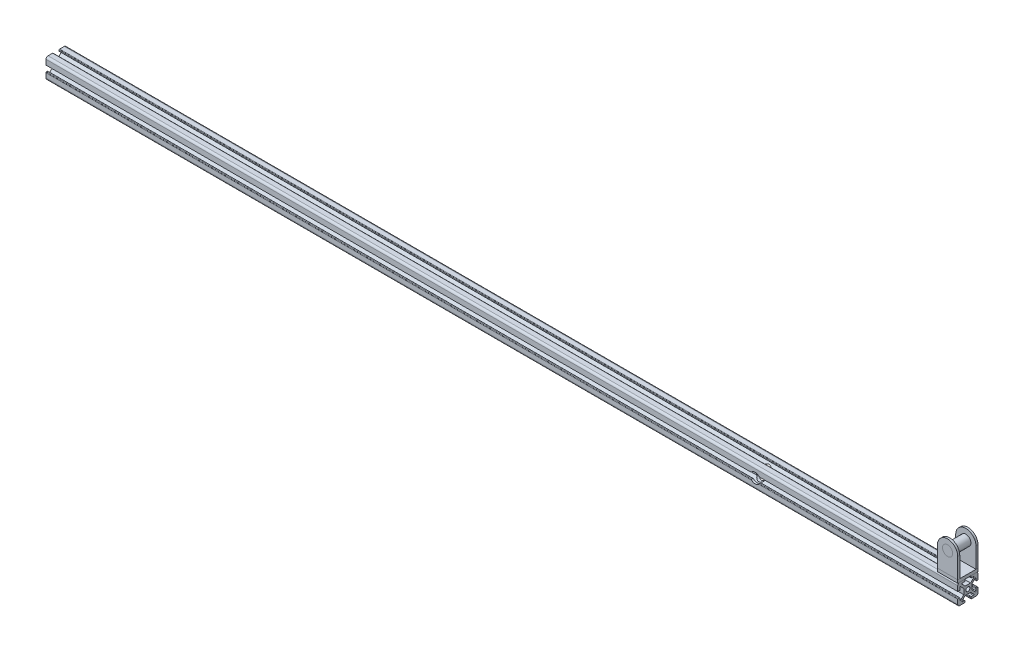
SolidWorks part; units mm, degrees
ref_plane "Front Plane" through (0, 0, 0) normal (0, 0, 1) x (1, 0, 0)
ref_plane "Top Plane" through (0, 0, 0) normal (0, 1, 0) x (1, 0, 0)
ref_plane "Right Plane" through (0, 0, 0) normal (1, 0, 0) x (0, 0, -1)
sketch "Sketch1" plane through (0, 0, 0) normal (0, 0, 1) x (1, 0, 0)
  line L0 (0, 0) -> (-1000, 0)
  point P3 (-200, 0)
  dimension "D1" = 800
  dimension "D2" = 200
other "Aluminium profile 20×20(1)"
ref_plane "Plane2" through (0, 0, 0) normal (-1, 0, 0) x (0, -1, 0)
sketch "Sketch2" plane through (0, 0, 0) normal (-1, 0, 0) x (0, -1, 0)
  line L1 (-2.6666, -4) -> (2.6666, -4)
  line L2 (-4, -2.6502) -> (-4, 2.6502)
  line L3 (-2.6666, 4) -> (2.6666, 4)
  line L4 (4, -2.6502) -> (4, 2.6502)
  line L9 (3.4986, 10) -> (7.9986, 10) construction
  line L10 (9.9986, 3.5) -> (9.9986, 8) construction
  line L11 (4, 2.6502) -> (7.1467, 5.7673)
  line L12 (2.6666, 4) -> (5.7766, 7.1486)
  line L13 (9.9986, 8) -> (9.9986, 3.5)
  line L14 (9.4986, 3) -> (8.4986, 3)
  line L15 (7.9986, 3.5) -> (7.9986, 5.4121)
  line L16 (7.9986, 10) -> (3.4986, 10)
  line L17 (2.9986, 9.5) -> (2.9986, 8.5)
  line L18 (3.4986, 8) -> (5.4209, 8)
  line L20 (-9.9986, 3.5) -> (-9.9986, 8) construction
  line L21 (-2.9986, 10) -> (-7.9986, 10) construction
  line L23 (-2.9986, 8) -> (-5.4209, 8)
  line L24 (-2.9986, 10) -> (-2.9986, 8)
  line L25 (-7.9986, 10) -> (-2.9986, 10)
  line L26 (-7.9986, 3.5) -> (-7.9986, 5.4121)
  line L27 (-9.4986, 3) -> (-8.4986, 3)
  line L28 (-9.9986, 8) -> (-9.9986, 3.5)
  line L29 (-2.6666, 4) -> (-5.7766, 7.1486)
  line L30 (-4, 2.6502) -> (-7.1467, 5.7673)
  line L32 (-3.4986, -10) -> (-7.9986, -10) construction
  line L33 (-9.9986, -3.5) -> (-9.9986, -8) construction
  line L34 (9.9986, -3.5) -> (9.9986, -8) construction
  line L35 (3.4986, -10) -> (7.9986, -10) construction
  line L37 (-4, -2.6502) -> (-7.1467, -5.7673)
  line L38 (-2.6666, -4) -> (-5.7766, -7.1486)
  line L39 (-9.9986, -8) -> (-9.9986, -3.5)
  line L40 (-9.4986, -3) -> (-8.4986, -3)
  line L41 (-7.9986, -3.5) -> (-7.9986, -5.4121)
  line L42 (-7.9986, -10) -> (-3.4986, -10)
  line L43 (-2.9986, -9.5) -> (-2.9986, -8.5)
  line L44 (-3.4986, -8) -> (-5.4209, -8)
  line L45 (3.4986, -8) -> (5.4209, -8)
  line L46 (2.9986, -9.5) -> (2.9986, -8.5)
  line L47 (7.9986, -10) -> (3.4986, -10)
  line L48 (7.9986, -3.5) -> (7.9986, -5.4121)
  line L49 (9.4986, -3) -> (8.4986, -3)
  line L50 (9.9986, -8) -> (9.9986, -3.5)
  line L51 (2.6666, -4) -> (5.7766, -7.1486)
  line L52 (4, -2.6502) -> (7.1467, -5.7673)
  circle A0 centre (0, 0) radius 2
  arc A1 (7.9986, -10) -> (9.9986, -8) centre (7.9986, -8) ccw
  arc A2 (-9.9986, -8) -> (-7.9986, -10) centre (-7.9986, -8) ccw
  arc A3 (-7.9986, 10) -> (-9.9986, 8) centre (-7.9986, 8) ccw
  arc A4 (7.9986, 10) -> (9.9986, 8) centre (7.9986, 8) cw
  arc A5 (-9.4986, -3) -> (-9.9986, -3.5) centre (-9.4986, -3.5) ccw
  arc A6 (-8.4986, -3) -> (-7.9986, -3.5) centre (-8.4986, -3.5) cw
  arc A7 (-7.1467, -5.7673) -> (-7.9986, -5.4121) centre (-7.4986, -5.4121) cw
  arc A8 (-5.7766, -7.1486) -> (-5.4209, -8) centre (-5.4209, -7.5) ccw
  arc A9 (-2.9986, -9.5) -> (-3.4986, -10) centre (-3.4986, -9.5) cw
  arc A10 (-2.9986, -8.5) -> (-3.4986, -8) centre (-3.4986, -8.5) ccw
  arc A11 (7.9986, -5.4121) -> (7.1467, -5.7673) centre (7.4986, -5.4121) cw
  arc A12 (5.4209, -8) -> (5.7766, -7.1486) centre (5.4209, -7.5) ccw
  arc A13 (3.4986, -8) -> (2.9986, -8.5) centre (3.4986, -8.5) ccw
  arc A14 (3.4986, -10) -> (2.9986, -9.5) centre (3.4986, -9.5) cw
  arc A15 (9.9986, -3.5) -> (9.4986, -3) centre (9.4986, -3.5) ccw
  arc A16 (7.9986, -3.5) -> (8.4986, -3) centre (8.4986, -3.5) cw
  arc A17 (9.9986, 3.5) -> (9.4986, 3) centre (9.4986, 3.5) cw
  arc A18 (8.4986, 3) -> (7.9986, 3.5) centre (8.4986, 3.5) cw
  arc A19 (7.9986, 5.4121) -> (7.1467, 5.7673) centre (7.4986, 5.4121) ccw
  arc A20 (3.4986, 10) -> (2.9986, 9.5) centre (3.4986, 9.5) ccw
  arc A21 (2.9986, 8.5) -> (3.4986, 8) centre (3.4986, 8.5) ccw
  arc A22 (5.4209, 8) -> (5.7766, 7.1486) centre (5.4209, 7.5) cw
  arc A23 (-5.4209, 8) -> (-5.7766, 7.1486) centre (-5.4209, 7.5) ccw
  arc A24 (-7.9986, 5.4121) -> (-7.1467, 5.7673) centre (-7.4986, 5.4121) cw
  arc A25 (-7.9986, 3.5) -> (-8.4986, 3) centre (-8.4986, 3.5) cw
  arc A26 (-9.9986, 3.5) -> (-9.4986, 3) centre (-9.4986, 3.5) ccw
  point P7 (0, 0)
  point P84 (7.9986, 3)
  point P92 (2.9986, 8)
  dimension "D1" = 4
  dimension "D2" = 2
  dimension "D3" = 0.5
sketch "Sketch3" plane through (0, 0, 10) normal (0, 0, 1) x (1, 0, 0)
  line L0 (0, 0) -> (-300, 0) construction
  circle A0 centre (-300, 0) radius 5
  dimension "D2" = 10
  dimension "D1" = 300
extrude "Cut-Extrude1" cut sketch "Sketch3" against normal blind 50 contours A0
sketch "Sketch10" plane through (0, 0, 0) normal (1, 0, 0) x (0, 0, -1)
  line L1 (-26.5936, -18.5268) -> (26.5936, -18.5268)
  line L2 (-26.5936, -18.5268) -> (-26.5936, 18.5268)
  line L3 (-26.5936, 18.5268) -> (26.5936, 18.5268)
  line L4 (26.5936, -18.5268) -> (26.5936, 18.5268)
  line L5 (-26.5936, -18.5268) -> (26.5936, 18.5268) construction
  line L6 (-26.5936, 18.5268) -> (26.5936, -18.5268) construction
  point P0 (0, 0)
extrude "Cut-Extrude5" cut sketch "Sketch10" against normal blind 100
sketch "Sketch14" plane through (0, 9.9986, 0) normal (0, 1, 0) x (1, 0, 0)
  line L0 (-1000, -10) -> (-100, -10) construction
  line L1 (-100, 10) -> (-120, 10)
  line L2 (-100, 10) -> (-100, -10)
  line L3 (-100, -10) -> (-120, -10)
  line L4 (-120, 10) -> (-120, -10)
  dimension "D1" = 20
  dimension "D2" = 20
extrude "Boss-Extrude3" add sketch "Sketch14" along normal blind 3 separate body
sketch "Sketch16" plane through (0, 0, 10) normal (0, 0, 1) x (1, 0, 0)
  line L1 (-120, 12.9986) -> (-100, 12.9986)
  line L2 (-120, 12.9986) -> (-120, 32.9986)
  line L4 (-100, 12.9986) -> (-100, 32.9986)
  arc A0 (-120, 32.9986) -> (-100, 32.9986) centre (-110, 32.9986) cw
  circle A1 centre (-110, 32.9986) radius 5
  dimension "D3" = 10
  dimension "D1" = 20
  dimension "D2" = 20
extrude "Boss-Extrude4" add sketch "Sketch16" against normal blind 2 separate body
sketch "Sketch17" plane through (0, 0, -10) normal (0, 0, -1) x (-1, 0, 0)
  line L0 (120, 32.9986) -> (120, 12.9986) construction
  line L1 (100, 12.9986) -> (120, 12.9986)
  line L2 (100, 12.9986) -> (100, 32.9584)
  line L4 (120, 12.9986) -> (120, 32.9584)
  arc A0 (100, 32.9584) -> (120, 32.9584) centre (110, 32.9584) cw
  circle A1 centre (110, 32.9584) radius 5.0402
extrude "Boss-Extrude5" add sketch "Sketch17" against normal blind 2 separate body
sketch "Sketch18" plane through (0, 0, -10) normal (0, 0, -1) x (-1, 0, 0)
  circle A0 centre (110, 32.9986) radius 5
extrude "Boss-Extrude6" add sketch "Sketch18" against normal blind 20 separate body
